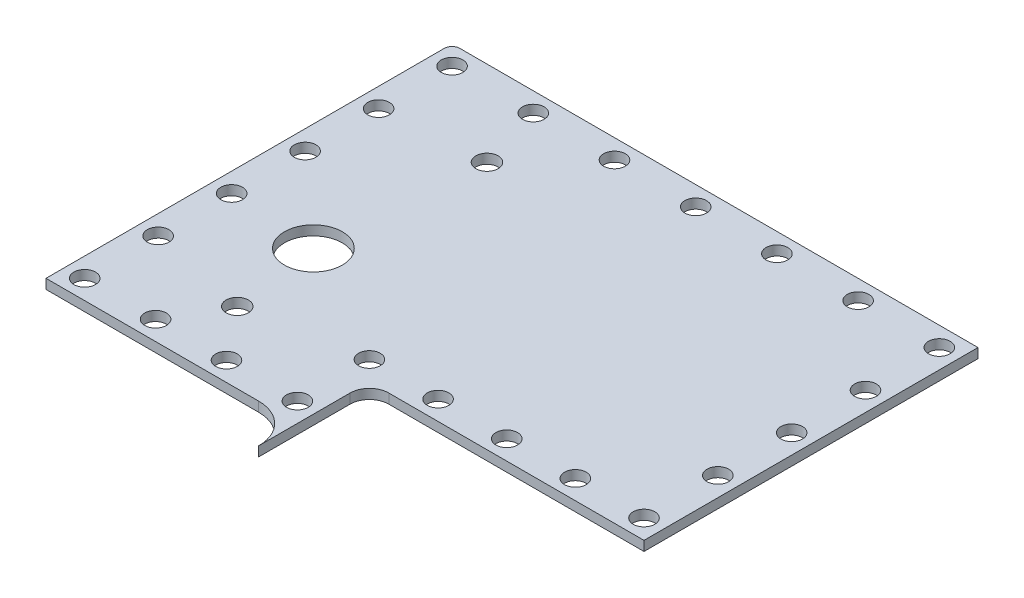
SolidWorks part; units mm, degrees
material "Zoltek Panex 33"
ref_plane "Front Plane" through (0, 0, 0) normal (0, 0, 1) x (1, 0, 0)
ref_plane "Top Plane" through (0, 0, 0) normal (0, 1, 0) x (1, 0, 0)
ref_plane "Right Plane" through (0, 0, 0) normal (1, 0, 0) x (0, 0, -1)
other "Bounding Box"
ref_plane "Default Plane" through (-8.9266, -12.7485, 0) normal (-0.1736, 0.9848, 0) x (0.9848, 0.1736, 0)
sketch "Sketch1" plane through (0, 0, 0) normal (0, 1, 0) x (1, 0, 0)
  line B0 (-8.89, -66.675) -> (-43.815, -66.675)
  line B1 (-43.815, -66.675) -> (-43.815, -1.27)
  line B2 (-42.545, 0) -> (42.545, 0)
  line B3 (42.545, 0) -> (42.545, -54.8431)
  line B4 (42.545, -54.8431) -> (-2.54, -54.8431)
  line B5 (-2.54, -54.8431) -> (-2.54, -73.025)
  arc B6 (-2.54, -73.025) -> (-8.89, -66.675) centre (-8.89, -73.025) ccw
  arc B7 (-42.545, 0) -> (-43.815, -1.27) centre (-42.545, -1.27) ccw
sketch_block_instance "Right Side sketch block-1"
sketch_block "Right Side sketch block"
extrude "Boss-Extrude1" add sketch "Sketch1" along normal blind 1.5875
fillet "Fillet1" radius 3.175 1 edges at (-2.54, 0.7937, 54.8431)
sketch "Sketch2" plane through (0, 1.5875, 0) normal (0, 1, 0) x (-1, 0, 0)
  line L0 (43.815, 1.27) -> (43.815, 66.675) construction
  line L1 (-42.545, 0) -> (42.545, 0) construction
  circle A0 centre (26.115, 40.4703) radius 4.75
  circle A1 centre (24.115, 54.9704) radius 1.83
  circle A2 centre (24.1149, 13.97) radius 1.83
  line B0 (21.0839, 12.2202) -> (17.115, 19.4702)
  line B1 (17.115, 19.4702) -> (17.115, 49.4704)
  line B2 (17.115, 49.4704) -> (21.0839, 56.7204)
  line B3 (31.115, 49.4704) -> (27.1461, 56.7204)
  line B4 (31.115, 49.4704) -> (31.115, 19.4702)
  line B5 (31.115, 19.4702) -> (27.1461, 12.2202)
  circle B6 centre (24.1149, 13.97) radius 1.83
  circle B7 centre (24.115, 54.9704) radius 1.83
  circle B8 centre (26.115, 40.4703) radius 4.75
  arc B9 (21.0839, 12.2202) -> (27.1461, 12.2202) centre (24.115, 13.9702) ccw
  arc B10 (27.1461, 56.7204) -> (21.0839, 56.7204) centre (24.115, 54.9705) ccw
  dimension "D1" = 12.7
  dimension "D2" = 13.97
sketch_block_instance "Switch+PD+Bord+V1-1"
sketch_block "Switch+PD+Bord+V1" parameters "D1"=9.5001, "D2"=3.66, "D3"=3.5
extrude "Cut-Extrude1" cut sketch "Sketch2" against normal through all both and the other way through all contours A0 | A1 | A2
sketch "Sketch3" plane through (0, 1.5875, 0) normal (0, 1, 0) x (-1, 0, 0)
  line L0 (-39.37, 3.175) -> (-39.37, 51.6681) construction
  line L1 (-39.37, 51.6681) -> (5.715, 51.6681) construction
  line L2 (5.715, 51.6681) -> (5.715, 63.5) construction
  line L3 (5.715, 63.5) -> (40.64, 63.5) construction
  line L4 (40.64, 63.5) -> (40.64, 3.175) construction
  line L5 (40.64, 3.175) -> (-39.37, 3.175) construction
  line L6 (-42.545, 0) -> (42.545, 0) construction
  line L7 (43.815, 1.27) -> (43.815, 66.675) construction
  line L8 (43.815, 66.675) -> (8.89, 66.675) construction
  line L9 (2.54, 73.025) -> (2.54, 58.0181) construction
  line L10 (-0.635, 54.8431) -> (-42.545, 54.8431) construction
  line L11 (-42.545, 54.8431) -> (-42.545, 0) construction
  circle A1 centre (27.305, 3.175) radius 1.778
  circle A2 centre (13.97, 3.175) radius 1.778
  circle A3 centre (0.635, 3.175) radius 1.778
  circle A4 centre (-12.7, 3.175) radius 1.778
  circle A5 centre (-26.035, 3.175) radius 1.778
  circle A6 centre (-39.37, 3.175) radius 1.778
  circle A7 centre (-39.37, 15.2983) radius 1.778
  circle A8 centre (-39.37, 27.4215) radius 1.778
  circle A9 centre (-39.37, 39.5448) radius 1.778
  circle A10 centre (-39.37, 51.6681) radius 1.778
  circle A11 centre (-28.0987, 51.6681) radius 1.778
  circle A12 centre (-16.8275, 51.6681) radius 1.778
  circle A13 centre (-5.5562, 51.6681) radius 1.778
  circle A14 centre (5.715, 51.6681) radius 1.778
  circle A15 centre (5.715, 63.5) radius 1.778
  circle A16 centre (17.3567, 63.5) radius 1.778
  circle A17 centre (28.9983, 63.5) radius 1.778
  circle A18 centre (40.64, 63.5) radius 1.778
  circle A19 centre (40.64, 51.435) radius 1.778
  circle A20 centre (40.64, 39.37) radius 1.778
  circle A21 centre (40.64, 27.305) radius 1.778
  circle A22 centre (40.64, 15.24) radius 1.778
  circle A24 centre (40.64, 3.175) radius 1.778 [skipped]
  circle A25 centre (40.64, 3.175) radius 1.778
  dimension "D7" = 3.556
  dimension "D14" = 13.335
  dimension "D15" = 13.335
  dimension "D18" = 13.335
  dimension "D1" = 3.175
  dimension "D2" = 3.175
  dimension "D3" = 3.175
  dimension "D4" = 3.175
  dimension "D5" = 3.175
  dimension "D6" = 3.175
  dimension "D8" = 12.065
  dimension "D16" = 13.335
  dimension "D17" = 13.335
  dimension "D9" = 5
  dimension "D10" = 5
  dimension "D11" = 2
  dimension "D12" = 4
  dimension "D13" = 6
extrude "Cut-Extrude2" cut sketch "Sketch3" against normal through all both and the other way through all
